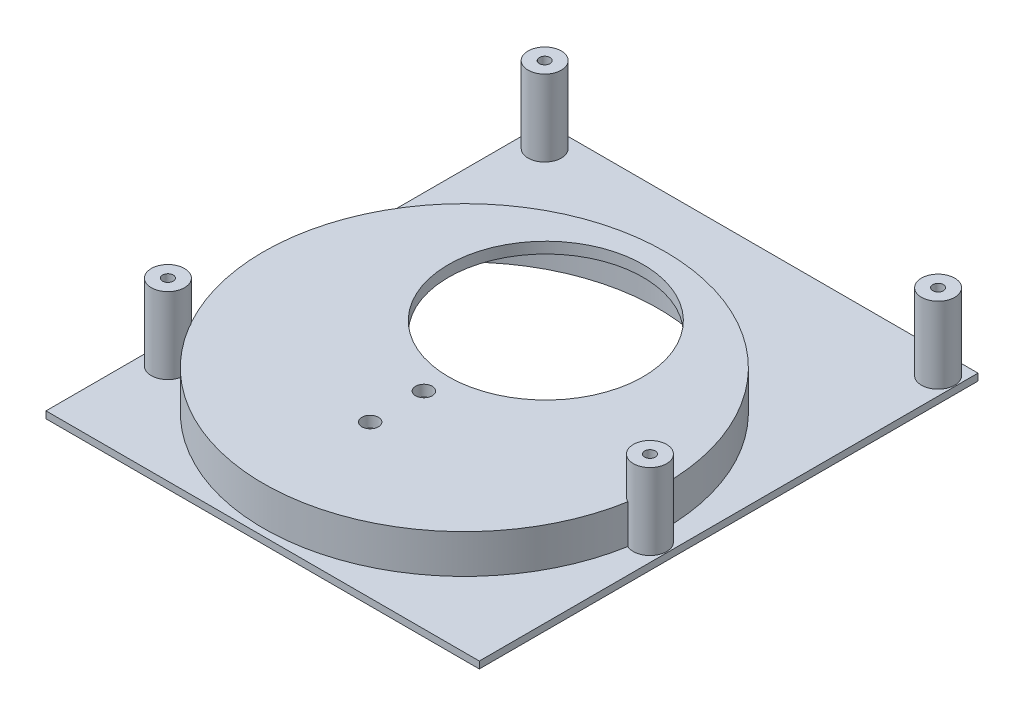
SolidWorks part; units mm, degrees
ref_plane "Front Plane" through (0, 0, 0) normal (0, 0, 1) x (1, 0, 0)
ref_plane "Top Plane" through (0, 0, 0) normal (0, 1, 0) x (1, 0, 0)
ref_plane "Right Plane" through (0, 0, 0) normal (1, 0, 0) x (0, 0, -1)
sketch "Sketch1" plane through (0, 0, 0) normal (0, 1, 0) x (1, 0, 0)
  line L2 (-81.3883, 93.7433) -> (-81.3883, -20.5567)
  line L3 (-81.3883, -20.5567) -> (17.9257, -20.5567)
  line L4 (17.9257, 93.7433) -> (17.9257, -20.5567)
  line L5 (-66.3714, -17.3817) -> (-19.3204, -17.3817) construction
  line L7 (15.3857, 88.6633) -> (15.3857, 22.6233) construction
  line L9 (-81.3883, 93.7433) -> (17.9257, 93.7433)
  line L14 (106.5717, 91.2033) -> (-78.8483, 91.2033) construction
  line L15 (-78.8483, 91.2033) -> (-78.8483, -0.2367) construction
  circle A0 centre (-33.1283, 27.0683) radius 44.45 construction
  circle A2 centre (13.8617, 88.6633) radius 1.524 construction
  circle A3 centre (13.8617, 22.6233) radius 1.524 construction
  dimension "D1" = 3.175
  dimension "D2" = 2.54
  dimension "D3" = 2.54
  dimension "D4" = 2.54
extrude "main" add sketch "Sketch1" along normal blind 1.5875
sketch "Sketch3" plane through (0, 0, 0) normal (0, 1, 0) x (1, 0, 0)
  circle A2 centre (-33.1283, 27.0683) radius 44.45 construction
  circle A3 centre (-33.1283, 27.0683) radius 46.0375
  circle A4 centre (-33.1283, 27.0683) radius 44.45 construction
  dimension "D1" = 1.5875
extrude "raised disk edge" add sketch "Sketch3" along normal offset from surface (10.4775 mm away) 2.54 separate body
sketch "Sketch4" plane through (0, 7.9375, 0) normal (0, 1, 0) x (1, 0, 0)
  circle A0 centre (-33.1283, 27.0683) radius 44.45
  circle A1 centre (-33.1283, 27.0683) radius 46.0375 construction
  dimension "D1" = 1.5875
extrude "disk hollow" cut sketch "Sketch4" against normal through all
sketch "Sketch5" plane through (0, 10.4775, 0) normal (0, 1, 0) x (1, 0, 0)
  circle A0 centre (-33.1283, 17.7973) radius 1.905
  circle A1 centre (-33.1283, 5.4783) radius 1.905
  circle A2 centre (-33.1283, 5.4783) radius 1.651 construction
  circle A3 centre (-33.1283, 17.7973) radius 1.651 construction
  dimension "D1" = 0.254
  dimension "D2" = 0.254
extrude "screw holes on front panel" cut sketch "Sketch5" against normal up to next (2.54 mm away)
sketch "Sketch6" plane through (0, 1.5875, 0) normal (0, 1, 0) x (1, 0, 0)
  circle A0 centre (-76.3083, 2.3033) radius 3.81
  circle A1 centre (13.8617, 22.6233) radius 3.81
  circle A2 centre (-76.3083, 88.6633) radius 3.81
  circle A3 centre (13.8617, 88.6633) radius 3.81
  circle A4 centre (-76.3083, 88.6633) radius 1.524 construction
  circle A5 centre (13.8617, 88.6633) radius 1.524 construction
  circle A6 centre (-76.3083, 2.3033) radius 1.524 construction
  circle A7 centre (13.8617, 22.6233) radius 1.524 construction
  circle A8 centre (-76.3083, 88.6633) radius 1.224
  circle A9 centre (13.8617, 88.6633) radius 1.224
  circle A10 centre (13.8617, 22.6233) radius 1.224
  circle A11 centre (-76.3083, 2.3033) radius 1.224
  dimension "D1" = 7.62
  dimension "D2" = 2.4479
extrude "mounting posts" add sketch "Sketch6" along normal up to surface (17.4625 mm away)
sketch "Sketch8" plane through (0, 10.4775, 0) normal (0, 1, 0) x (1, 0, 0)
  line L0 (-33.1283, 45.7373) -> (-33.1283, 5.4783) construction
  line L1 (-33.1283, 17.7973) -> (-33.1283, 5.4783) construction
  circle A0 centre (-33.1283, 45.7373) radius 22.2979
  dimension "D1" = 27.94
extrude "hollow" cut sketch "Sketch8" against normal up to next
sketch "Sketch9" plane through (0, 1.5875, 0) normal (0, 1, 0) x (1, 0, 0)
  line L1 (-74.7712, 85.0879) -> (-73.4713, 85.9992) construction
  line L2 (-74.7712, 85.0879) -> (-60.2051, 64.3098)
  line L3 (-60.2051, 64.3098) -> (-58.9052, 65.2211) construction
  line L4 (-73.4713, 85.9992) -> (-58.9052, 65.2211)
  arc A0 (-73.4713, 85.9992) -> (-74.7712, 85.0879) centre (-74.1213, 85.5436) ccw
  arc A1 (-60.2051, 64.3098) -> (-58.9052, 65.2211) centre (-59.5552, 64.7655) ccw
  circle A4 centre (-33.1283, 27.0683) radius 46.0375 construction
  circle A5 centre (-76.3083, 88.6633) radius 3.81 construction
  point P10 (-59.5552, 64.7655)
  point P11 (-74.1213, 85.5436)
  dimension "D1" = 1.5875
extrude "cross braces" [suppressed] add sketch "Sketch9" along normal up to surface (8.89 mm away)
